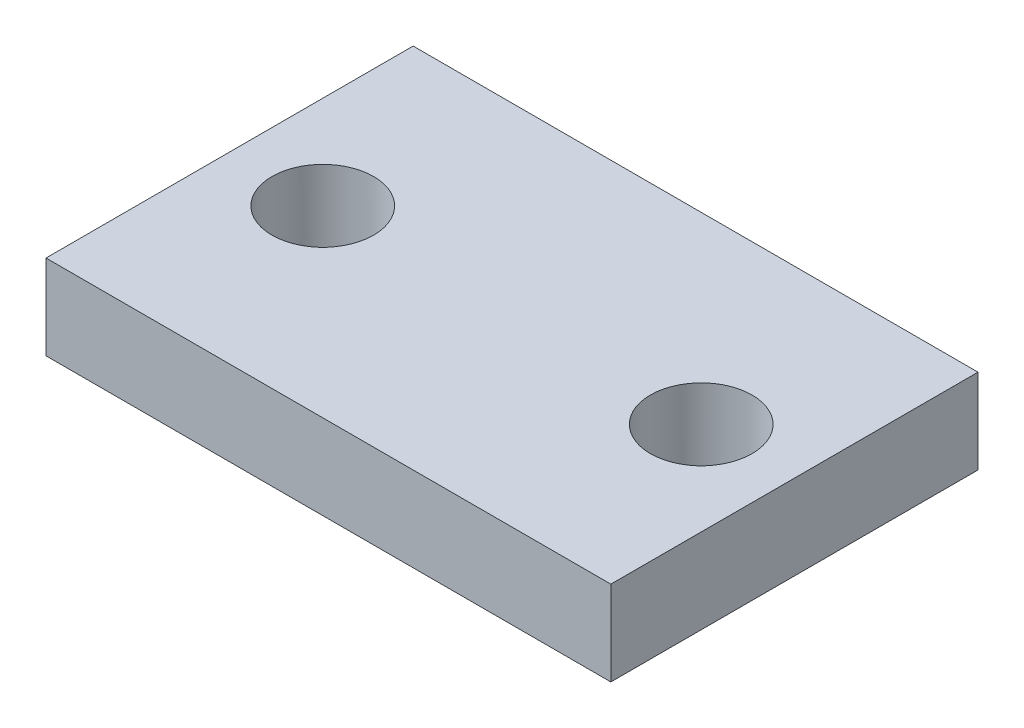
SolidWorks part; units mm, degrees
ref_plane "Front Plane" through (0, 0, 0) normal (0, 0, 1) x (1, 0, 0)
ref_plane "Top Plane" through (0, 0, 0) normal (0, 1, 0) x (1, 0, 0)
ref_plane "Right Plane" through (0, 0, 0) normal (1, 0, 0) x (0, 0, -1)
sketch "Sketch1" plane through (0, 0, 0) normal (0, 1, 0) x (1, 0, 0)
  line L1 (0, 0) -> (20, 0)
  line L2 (0, 0) -> (0, 13)
  line L3 (0, 13) -> (20, 13)
  line L4 (20, 0) -> (20, 13)
  dimension "D1" = 13
  dimension "D2" = 20
extrude "Boss-Extrude1" add sketch "Sketch1" along normal blind 3
sketch "Sketch2" plane through (0, 3, 0) normal (0, 1, 0) x (1, 0, 0)
  circle A0 centre (3.3, 6.5) radius 1.8 construction
  circle A1 centre (16.7, 6.5) radius 1.8 construction
  circle A2 centre (3.3, 6.5) radius 1.8
  circle A3 centre (16.7, 6.5) radius 1.8
extrude "Cut-Extrude1" cut sketch "Sketch2" against normal through all both and the other way through all
